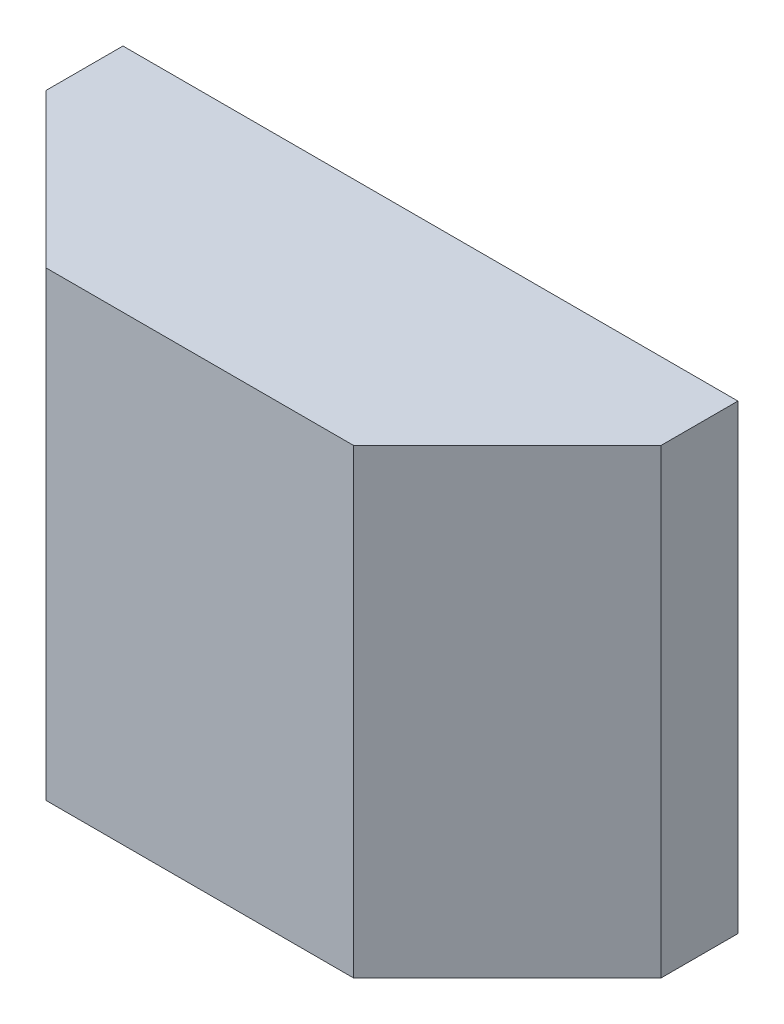
SolidWorks part; units mm, degrees
ref_plane "Спереди" through (0, 0, 0) normal (0, 0, 1) x (1, 0, 0)
ref_plane "Сверху" through (0, 0, 0) normal (0, 1, 0) x (1, 0, 0)
ref_plane "Справа" through (0, 0, 0) normal (1, 0, 0) x (0, 0, -1)
sketch "Эскиз1" plane through (0, 0, 0) normal (0, 0, 1) x (1, 0, 0)
  line L1 (-2, -1.5) -> (2, -1.5)
  line L2 (-2, -1.5) -> (-2, 1.5)
  line L3 (-2, 1.5) -> (2, 1.5)
  line L4 (2, -1.5) -> (2, 1.5)
  line L5 (-2, -1.5) -> (2, 1.5) construction
  line L6 (-2, 1.5) -> (2, -1.5) construction
  point P0 (0, 0)
  dimension "D1" = 4
  dimension "D2" = 3
extrude "Бобышка-Вытянуть1" add sketch "Эскиз1" along normal blind 1.5
chamfer "Фаска1" distance 1 angle 45 2 edges at (2, 0, 1.5) (-2, 0, 1.5)
